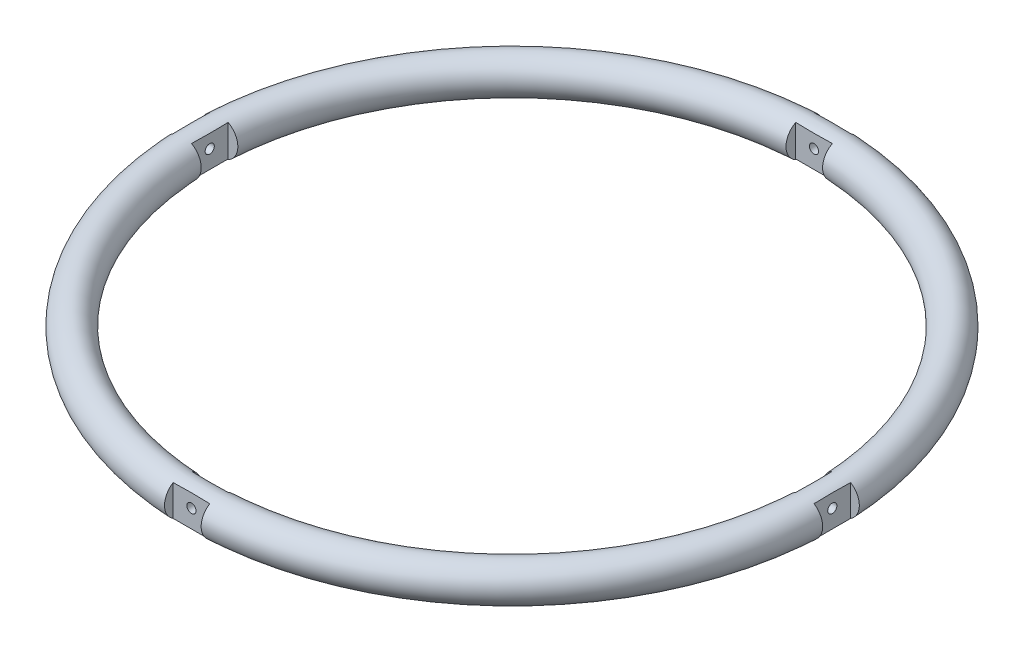
SolidWorks part; units mm, degrees
material "Cast Carbon Steel"
ref_plane "Front Plane" through (0, 0, 0) normal (0, 0, 1) x (1, 0, 0)
ref_plane "Top Plane" through (0, 0, 0) normal (0, 1, 0) x (1, 0, 0)
ref_plane "Right Plane" through (0, 0, 0) normal (1, 0, 0) x (0, 0, -1)
sketch "Sketch1" plane through (0, 0, 0) normal (0, 0, 1) x (1, 0, 0)
  line L0 (0, 28.8872) -> (0, -28.8872) construction
  line L1 (-58.6678, 0) -> (58.6678, 0) construction
  circle A0 centre (68, 0) radius 4
  point P7 (0, 0)
  point P8 (0, 0)
  dimension "D1" = 8
  dimension "D2" = 68
revolve "Revolve1" add sketch "Sketch1" angle 360 about L0
ref_plane "Plane1" through (0, 4, 0) normal (0, 1, 0) x (1, 0, 0)
sketch "Sketch2" plane through (0, 4, 0) normal (0, 1, 0) x (1, 0, 0)
  line L1 (-66, -4) -> (66, -4)
  line L2 (-66, -4) -> (-66, 4)
  line L3 (-66, 4) -> (66, 4)
  line L4 (66, -4) -> (66, 4)
  line L5 (-66, -4) -> (66, 4) construction
  line L6 (-66, 4) -> (66, -4) construction
  line L7 (-4, -66) -> (4, -66)
  line L8 (-4, -66) -> (-4, 66)
  line L9 (-4, 66) -> (4, 66)
  line L10 (4, -66) -> (4, 66)
  line L11 (-4, -66) -> (4, 66) construction
  line L12 (-4, 66) -> (4, -66) construction
  point P0 (0, 0)
  point P6 (0, 0)
  dimension "D1" = 8
  dimension "D2" = 132
  dimension "D3" = 8
  dimension "D4" = 132
extrude "Cut-Extrude1" cut sketch "Sketch2" against normal through all contours L1 L8 L3 L2 | L3 L10 L9 L8 | L10 L1 L4 L3 | L7 L10 L1 L8 | L1 L10 L3 L8
sketch "Sketch3" plane through (0, 4, 0) normal (0, 1, 0) x (1, 0, 0)
  line L0 (66, 4) -> (66, -4) construction
  line L1 (70, -4) -> (75, -4)
  line L2 (70, -4) -> (70, 4)
  line L3 (70, 4) -> (75, 4)
  line L4 (75, -4) -> (75, 4)
  line L5 (66, -4) -> (63.8749, -4) construction
  dimension "D1" = 4
  dimension "D2" = 8
  dimension "D3" = 5
extrude "Cut-Extrude2" cut sketch "Sketch3" against normal through all
pattern_circular "CirPattern1" count 4 over 360 about axis through (0, 0, 0) along (0, 1, 0) of "Cut-Extrude2"
sketch "Sketch4" plane through (0, 0, 70) normal (0, 0, 1) x (1, 0, 0)
  line L4 (-4, -3.3956) -> (-4, -8.6318)
  line L5 (-4, -8.6318) -> (4, -8.6318)
  line L6 (4, -8.6318) -> (4, -3.3956)
  line L7 (4, -3.3956) -> (-4, -3.3956)
extrude "Cut-Extrude3" cut sketch "Sketch4" against normal through all
sketch "Sketch5" plane through (-70, 0, 0) normal (-1, 0, 0) x (0, 0, 1)
  line L0 (-4, -3.3956) -> (-4, -9.0805)
  line L1 (-4, -9.0805) -> (4, -9.0805)
  line L2 (4, -9.0805) -> (4, -3.3956)
  line L3 (4, -3.3956) -> (-4, -3.3956)
extrude "Cut-Extrude4" cut sketch "Sketch5" against normal through all
sketch "Sketch6" plane through (0, 0, -70) normal (0, 0, -1) x (-1, 0, 0)
  circle A0 centre (0.0079, 0.5296) radius 1
extrude "Cut-Extrude5" cut sketch "Sketch6" against normal through all
sketch "Sketch7" plane through (-70, 0, 0) normal (-1, 0, 0) x (0, 0, 1)
  circle A0 centre (0.0079, 0.5296) radius 1
extrude "Cut-Extrude6" cut sketch "Sketch7" against normal through all
